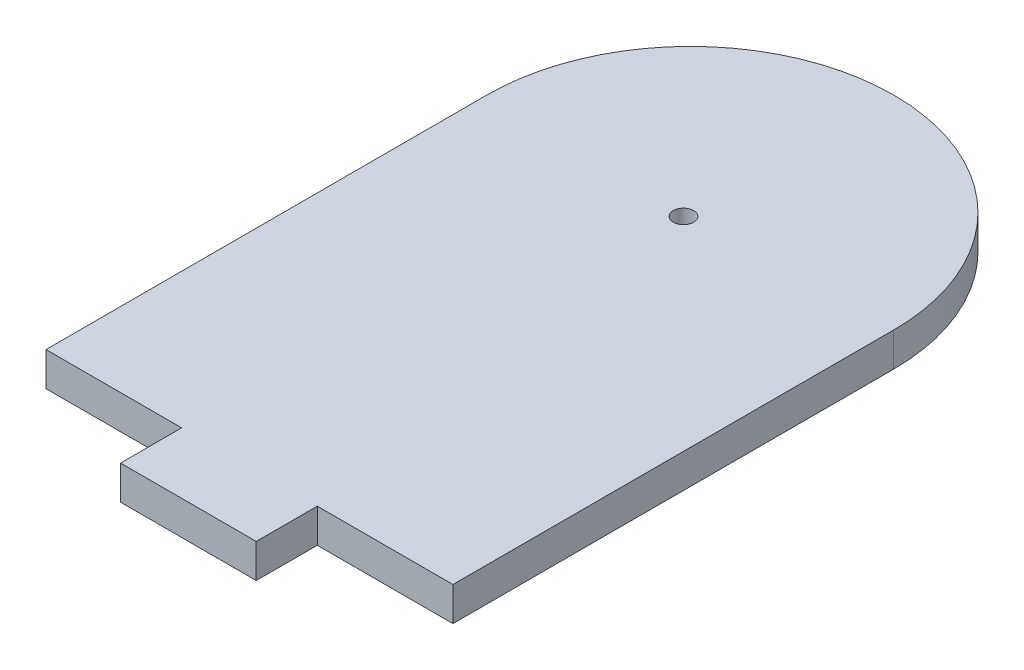
SolidWorks part; units mm, degrees
ref_plane "Front Plane" through (0, 0, 0) normal (0, 0, 1) x (1, 0, 0)
ref_plane "Top Plane" through (0, 0, 0) normal (0, 1, 0) x (1, 0, 0)
ref_plane "Right Plane" through (0, 0, 0) normal (1, 0, 0) x (0, 0, -1)
sketch "Sketch1" plane through (0, 0, 0) normal (0, 1, 0) x (1, 0, 0)
  line L0 (0, 32.5) -> (0, -32.5) construction
  line L1 (-30, -32.5) -> (30, -32.5)
  line L2 (-30, -32.5) -> (-30, 32.5)
  line L3 (-30, 32.5) -> (30, 32.5)
  line L4 (30, -32.5) -> (30, 32.5)
  line L5 (-30, -32.5) -> (30, 32.5) construction
  line L6 (-30, 32.5) -> (30, -32.5) construction
  line L7 (-30, 0) -> (30, 0) construction
  line L8 (-10, -32.5) -> (-10, -41.5)
  line L9 (-10, -41.5) -> (10, -41.5)
  line L10 (10, -41.5) -> (10, -32.5)
  line L11 (10, -32.5) -> (-10, -32.5)
  arc A0 (30, 32.5) -> (-30, 32.5) centre (0, 32.5) ccw
  point P0 (0, 0)
  dimension "D6" = 30
  dimension "D1" = 60
  dimension "D2" = 65
  dimension "D3" = 20
  dimension "D4" = 20
  dimension "D5" = 9
extrude "Boss-Extrude1" add sketch "Sketch1" along normal blind 5 contours L1 L4 L3 L2 | L9 L10 L1 L8 | L3 A0
sketch "Sketch2" plane through (0, 5, 0) normal (0, 1, 0) x (1, 0, 0)
  line L0 (-10, -41.5) -> (10, -41.5) construction
  line L1 (-30, -32.5) -> (-30, 32.5) construction
  circle A0 centre (0, 31.5) radius 1.5
  dimension "D1" = 3
  dimension "D3" = 30
  dimension "102.5" = 73
extrude "Cut-Extrude1" cut sketch "Sketch2" against normal through all
